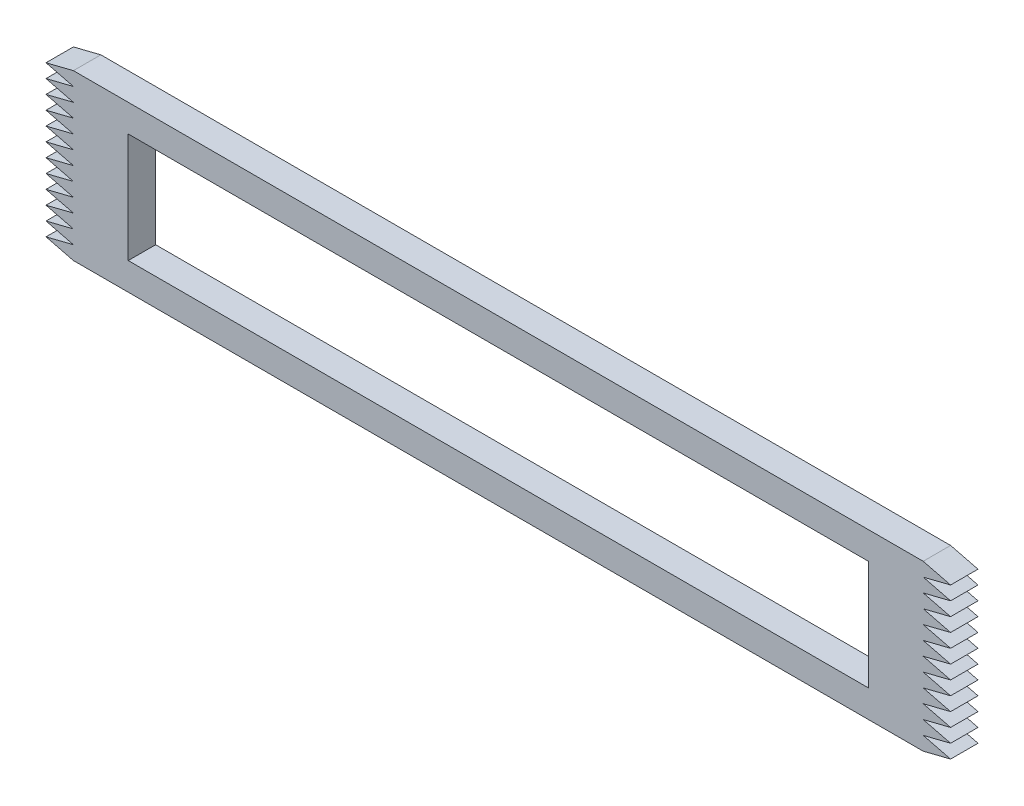
SolidWorks part; units mm, degrees
ref_plane "Front Plane" through (0, 0, 0) normal (0, 0, 1) x (1, 0, 0)
ref_plane "Top Plane" through (0, 0, 0) normal (0, 1, 0) x (1, 0, 0)
ref_plane "Right Plane" through (0, 0, 0) normal (1, 0, 0) x (0, 0, -1)
sketch "Sketch1" plane through (0, 0, 0) normal (0, 0, 1) x (1, 0, 0)
  line L26 (-12.7, -6.35) -> (-19.05, -4.7625)
  line L73 (0, 0) -> (171.45, 0)
  line L74 (0, 0) -> (0, 25.4)
  line L75 (0, 25.4) -> (171.45, 25.4)
  line L76 (171.45, 0) -> (171.45, 25.4)
  line L77 (-12.7, -6.35) -> (184.15, -6.35)
  line L78 (-12.7, -6.35) -> (-12.7, 31.75) construction
  line L79 (-12.7, 31.75) -> (184.15, 31.75)
  line L80 (184.15, -6.35) -> (184.15, 31.75) construction
  line L81 (-19.05, -4.7625) -> (-12.7, -3.175)
  line L82 (-12.7, -3.175) -> (-19.05, -1.5875)
  line L83 (-19.05, -1.5875) -> (-12.7, 0)
  line L84 (-12.7, 0) -> (-19.05, 1.5875)
  line L85 (-19.05, 1.5875) -> (-12.7, 3.175)
  line L86 (-12.7, 3.175) -> (-19.05, 4.7625)
  line L87 (-19.05, 4.7625) -> (-12.7, 6.35)
  line L88 (-12.7, 6.35) -> (-19.05, 7.9375)
  line L89 (-19.05, 7.9375) -> (-12.7, 9.525)
  line L90 (-12.7, 9.525) -> (-19.05, 11.1125)
  line L91 (-19.05, 11.1125) -> (-12.7, 12.7)
  line L92 (-12.7, 12.7) -> (-19.05, 14.2875)
  line L93 (-19.05, 14.2875) -> (-12.7, 15.875)
  line L94 (-12.7, 15.875) -> (-19.05, 17.4625)
  line L95 (-19.05, 17.4625) -> (-12.7, 19.05)
  line L96 (-12.7, 19.05) -> (-19.05, 20.6375)
  line L97 (-19.05, 20.6375) -> (-12.7, 22.225)
  line L98 (-12.7, 22.225) -> (-19.05, 23.8125)
  line L99 (-19.05, 23.8125) -> (-12.7, 25.4)
  line L100 (-12.7, 25.4) -> (-19.05, 26.9875)
  line L101 (-19.05, 26.9875) -> (-12.7, 28.575)
  line L102 (-12.7, 28.575) -> (-19.05, 30.1625)
  line L103 (-19.05, 30.1625) -> (-12.7, 31.75)
  line L104 (85.725, 31.75) -> (85.725, -6.35) construction
  line L105 (190.5, 30.1625) -> (184.15, 31.75)
  line L106 (184.15, 28.575) -> (190.5, 30.1625)
  line L107 (190.5, 26.9875) -> (184.15, 28.575)
  line L108 (184.15, 25.4) -> (190.5, 26.9875)
  line L109 (190.5, 23.8125) -> (184.15, 25.4)
  line L110 (184.15, 22.225) -> (190.5, 23.8125)
  line L111 (190.5, 20.6375) -> (184.15, 22.225)
  line L112 (184.15, 19.05) -> (190.5, 20.6375)
  line L113 (190.5, 17.4625) -> (184.15, 19.05)
  line L114 (184.15, 15.875) -> (190.5, 17.4625)
  line L115 (190.5, 14.2875) -> (184.15, 15.875)
  line L116 (184.15, 12.7) -> (190.5, 14.2875)
  line L117 (190.5, 11.1125) -> (184.15, 12.7)
  line L118 (184.15, 9.525) -> (190.5, 11.1125)
  line L119 (190.5, 7.9375) -> (184.15, 9.525)
  line L120 (184.15, 6.35) -> (190.5, 7.9375)
  line L121 (190.5, 4.7625) -> (184.15, 6.35)
  line L122 (184.15, 3.175) -> (190.5, 4.7625)
  line L123 (184.15, 0) -> (190.5, 1.5875)
  line L124 (190.5, 1.5875) -> (184.15, 3.175)
  line L125 (190.5, -1.5875) -> (184.15, 0)
  line L126 (184.15, -3.175) -> (190.5, -1.5875)
  line L127 (190.5, -4.7625) -> (184.15, -3.175)
  line L128 (184.15, -6.35) -> (190.5, -4.7625)
  point P9 (-19.05, -4.7625)
  point P10 (-12.7, -3.175)
  dimension "D1" = 171.45
  dimension "D2" = 25.4
  dimension "D4" = 6.35
  dimension "D5" = 196.85
  dimension "D6" = 12.7
  dimension "D7" = 1.5875
  dimension "D8" = 1.5875
  dimension "D9" = 6.35
  dimension "D10" = 12
extrude "Boss-Extrude1" add sketch "Sketch1" along normal blind 6.35
